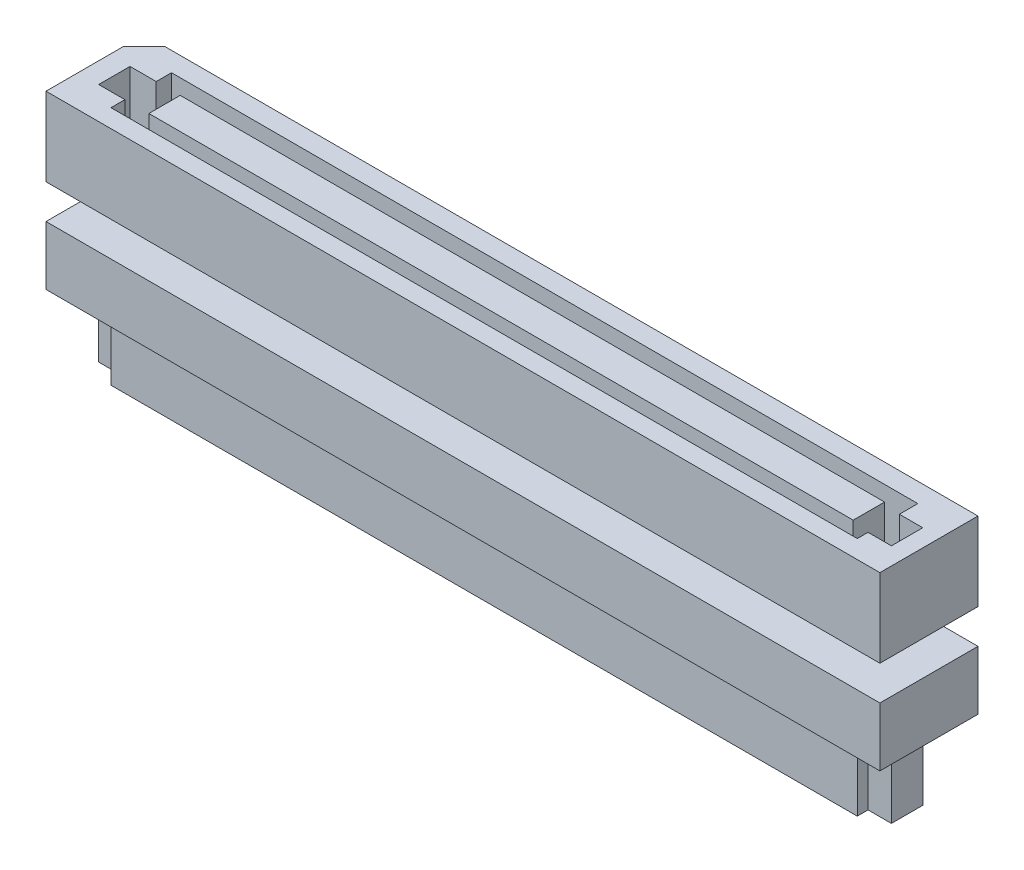
SolidWorks part; units mm, degrees
ref_plane "Front Plane" through (0, 0, 0) normal (0, 0, 1) x (1, 0, 0)
ref_plane "Top Plane" through (0, 0, 0) normal (0, 1, 0) x (1, 0, 0)
ref_plane "Right Plane" through (0, 0, 0) normal (1, 0, 0) x (0, 0, -1)
ref_plane "Plane1" through (0, -1.7526, 0) normal (0, 1, 0) x (1, 0, 0)
ref_plane "center-of-slot" through (0, -0.8763, 0) normal (0, 1, 0) x (1, 0, 0)
sketch "Sketch1" plane through (0, 0, 0) normal (0, 1, 0) x (1, 0, 0)
  line L13 (-20.189, 2.5) -> (21.25, 2.5)
  line L14 (-21.25, 1.439) -> (-21.25, -2.5)
  line L15 (-21.25, -2.5) -> (21.25, -2.5) construction
  line L16 (21.25, 2.5) -> (21.25, -2.5) construction
  line L20 (-21.25, 1.439) -> (-20.189, 2.5)
  line L33 (-21.25, -2.5) -> (20.19, -2.5)
  line L34 (20.19, -2.5) -> (21.25, -1.44) construction
  line L35 (21.25, -1.44) -> (21.25, 2.5)
  line L36 (20.19, -2.5) -> (21.25, -2.5)
  line L37 (21.25, -2.5) -> (21.25, -1.44)
  point P13 (-21.25, 2.5)
extrude "SV" add sketch "Sketch1" along normal blind 4
sketch "Sketch3" plane through (0, 4, 0) normal (0, 1, 0) x (1, 0, 0)
  line L60 (-20.2025, 0.7348) -> (-18.8675, 0.7348)
  line L61 (-20.2025, 1.5133) -> (20.3612, 1.5133) construction
  line L62 (-20.2025, 1.5133) -> (-20.2025, -1.5723) construction
  line L63 (-20.2025, -1.5723) -> (20.3612, -1.5723) construction
  line L64 (20.3612, 1.5133) -> (20.3612, -1.5723) construction
  line L65 (-18.8675, 0.7348) -> (-18.8675, 1.5133)
  line L66 (-18.8675, 1.5133) -> (19.1699, 1.5133)
  line L67 (19.1699, 1.5133) -> (19.1699, 0.5735)
  line L68 (19.1699, 0.5735) -> (20.3612, 0.5735)
  line L69 (20.3612, 0.5735) -> (20.3612, -1.0243)
  line L70 (20.3612, -1.0243) -> (19.1699, -1.0243)
  line L71 (19.1699, -1.0243) -> (19.1699, -1.5723)
  line L72 (19.1699, -1.5723) -> (-18.8675, -1.5723)
  line L73 (-18.8675, -1.5723) -> (-18.8675, -0.863)
  line L74 (-18.8675, -0.863) -> (-20.2025, -0.863)
  line L75 (-20.2025, -0.863) -> (-20.2025, 0.7348)
  line L76 (-17.6447, 0.7348) -> (18.253, 0.7348)
  line L77 (-17.6447, 0.7348) -> (-17.6447, -0.863)
  line L78 (-17.6447, -0.863) -> (18.253, -0.863)
  line L79 (18.253, 0.7348) -> (18.253, -0.863)
extrude "Cut-Extrude1" cut sketch "Sketch3" against normal blind 3.5
sketch "Sketch6" plane through (0, -1.7526, 0) normal (0, 1, 0) x (1, 0, 0)
  line L0 (21.25, -1.4381) -> (21.25, -2.5)
  line L1 (-21.25, 2.5) -> (21.25, 2.5) construction
  line L2 (-21.25, 2.5) -> (-21.25, -2.5) construction
  line L3 (-21.25, -2.5) -> (21.25, -2.5) construction
  line L4 (21.25, 2.5) -> (21.25, -2.5) construction
  line L5 (21.25, -2.5) -> (20.1881, -2.5)
  line L6 (-20.19, 2.5) -> (-21.25, 1.44)
  line L21 (21.25, -1.4381) -> (21.25, 2.5)
  line L22 (20.1881, -2.5) -> (-21.25, -2.5)
  line L33 (-21.25, -2.5) -> (-21.25, 1.44)
  line L34 (-21.25, 1.44) -> (-20.19, 2.5) construction
  line L35 (-20.19, 2.5) -> (21.25, 2.5)
  point P0 (-21.25, 2.5)
extrude "SV2(a)" add sketch "Sketch6" against normal blind 3 separate body
sketch "Sketch7" plane through (0, -4.7526, 0) normal (0, -1, 0) x (1, 0, 0)
  line L0 (-18.8675, -1.5133) -> (-18.8675, -0.7348)
  line L1 (-18.8675, -0.7348) -> (-20.2025, -0.7348)
  line L2 (-20.2025, -0.7348) -> (-20.2025, 0.863)
  line L3 (-20.2025, 0.863) -> (-18.8675, 0.863)
  line L4 (-18.8675, 0.863) -> (-18.8675, 1.5723)
  line L6 (-18.8675, 1.5723) -> (19.1699, 1.5723)
  line L7 (19.1699, 1.5723) -> (19.1699, 1.0243)
  line L8 (19.1699, 1.0243) -> (20.3612, 1.0243)
  line L9 (20.3612, 1.0243) -> (20.3612, -0.5735)
  line L10 (20.3612, -0.5735) -> (19.1699, -0.5735)
  line L11 (19.1699, -0.5735) -> (19.1699, -1.5133)
  line L12 (19.1699, -1.5133) -> (-18.8675, -1.5133)
  line L14 (-17.6447, -0.7348) -> (18.253, -0.7348)
  line L15 (-17.6447, -0.7348) -> (-17.6447, 0.863)
  line L16 (-17.6447, 0.863) -> (18.253, 0.863)
  line L17 (18.253, -0.7348) -> (18.253, 0.863)
extrude "SV2(b)" add sketch "Sketch7" along normal blind 3.5
